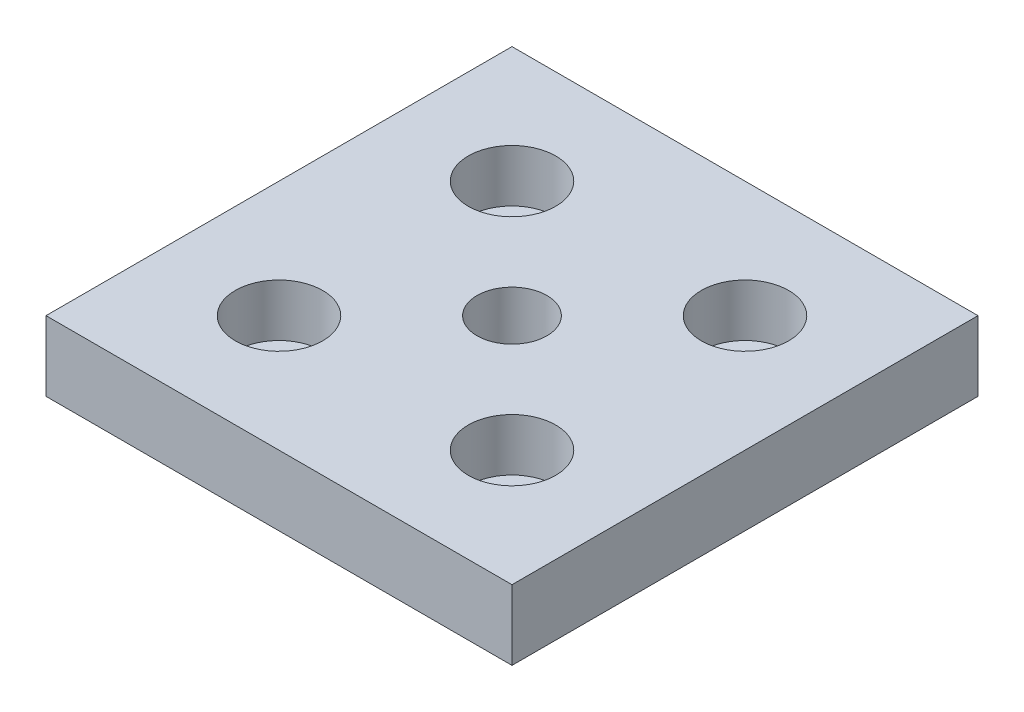
SolidWorks part; units mm, degrees
material "Алюминиевый сплав"
ref_plane "Спереди" through (0, 0, 0) normal (0, 0, 1) x (1, 0, 0)
ref_plane "Сверху" through (0, 0, 0) normal (0, 1, 0) x (1, 0, 0)
ref_plane "Справа" through (0, 0, 0) normal (1, 0, 0) x (0, 0, -1)
sketch "Эскиз1" plane through (0, 0, 0) normal (0, 1, 0) x (1, 0, 0)
  line L1 (-40, -40) -> (40, -40)
  line L2 (-40, -40) -> (-40, 40)
  line L3 (-40, 40) -> (40, 40)
  line L4 (40, -40) -> (40, 40)
  line L5 (-40, -40) -> (40, 40) construction
  line L6 (-40, 40) -> (40, -40) construction
  point P0 (0, 0)
  dimension "D1" = 80
extrude "Бобышка-Вытянуть1" add sketch "Эскиз1" along normal blind 12
hole_wizard "Отверстие обработанное метчиком M141" positions "Эскиз10" profile "Эскиз11" tap size "M14" standard "ISO" end condition up to next
sketch "Эскиз10" plane through (0, 12, 0) normal (0, 1, 0) x (1, 0, 0)
  point P0 (0, 0)
sketch "Эскиз11" plane through (0, 12, 0) normal (1, 0, 0) x (0, 0, 1)
  line L0 (0, 0) -> (0, 12)
  line L1 (0, 12) -> (6, 12)
  line L2 (6, 12) -> (6, 0)
  line L5 (6, 0) -> (0, 0)
  line L11 (0, -6.35) -> (0, 107.95) construction
  dimension "Диаметр проходного сверла" = 12
  dimension "Глубина проходного сверла" = 12
cosmetic thread "Отверстие резьбы4" parameters "D2"=14
sketch "Эскиз12" plane through (0, 12, 0) normal (0, 1, 0) x (1, 0, 0)
  line L1 (20, -20) -> (-20, -20) construction
  line L2 (20, -20) -> (20, 20) construction
  line L3 (20, 20) -> (-20, 20) construction
  line L4 (-20, -20) -> (-20, 20) construction
  line L5 (20, -20) -> (-20, 20) construction
  line L6 (20, 20) -> (-20, -20) construction
  circle A0 centre (-20, 20) radius 4.5
  circle A1 centre (20, 20) radius 4.5
  circle A2 centre (20, -20) radius 4.5
  circle A3 centre (-20, -20) radius 4.5
  point P0 (0, 0)
  dimension "D2" = 9
  dimension "D1" = 40
extrude "Вырез-Вытянуть1" cut sketch "Эскиз12" against normal through all
sketch "Эскиз13" plane through (0, 12, 0) normal (0, 1, 0) x (1, 0, 0)
  circle A0 centre (-20, 20) radius 7.5
  circle A1 centre (20, 20) radius 7.5
  circle A2 centre (20, -20) radius 7.5
  circle A3 centre (-20, -20) radius 7.5
  dimension "D1" = 15
extrude "Вырез-Вытянуть2" cut sketch "Эскиз13" against normal blind 9
